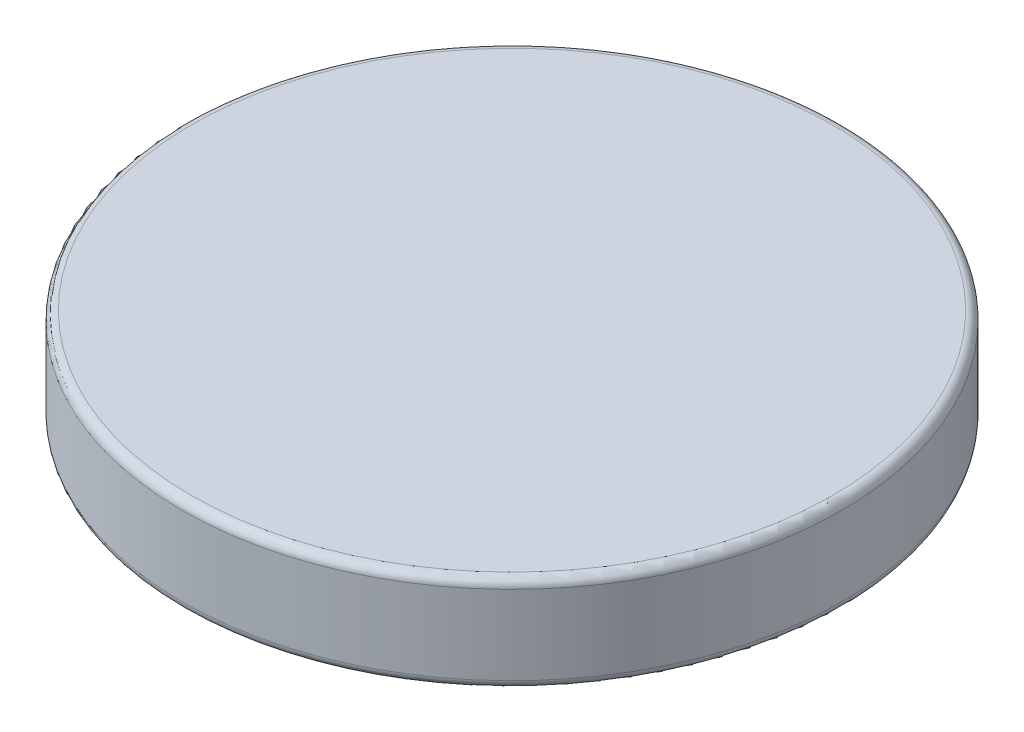
SolidWorks part; units mm, degrees
material "PE High Density"
ref_plane "Front Plane" through (0, 0, 0) normal (0, 0, 1) x (1, 0, 0)
ref_plane "Top Plane" through (0, 0, 0) normal (0, 1, 0) x (1, 0, 0)
ref_plane "Right Plane" through (0, 0, 0) normal (1, 0, 0) x (0, 0, -1)
sketch "Profile" plane through (0, 0, 0) normal (0, 1, 0) x (1, 0, 0)
  circle A0 centre (0, 0) radius 3.75
  dimension "D" = 7.5
extrude "Cap" add sketch "Profile" along normal blind 1.1
fillet "Production Fillet" radius 0.1 2 edges at (0, 0, 3.75) (0, 1.1, 3.75)
